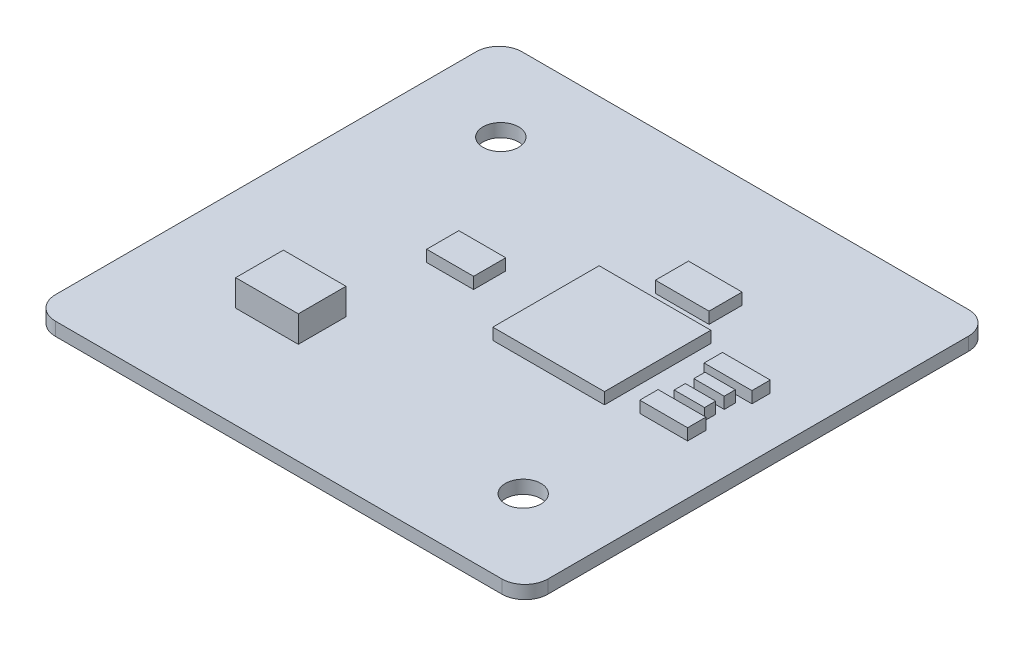
SolidWorks part; units mm, degrees
ref_plane "Front Plane" through (0, 0, 0) normal (0, 0, 1) x (1, 0, 0)
ref_plane "Top Plane" through (0, 0, 0) normal (0, 1, 0) x (1, 0, 0)
ref_plane "Right Plane" through (0, 0, 0) normal (1, 0, 0) x (0, 0, -1)
sketch "Sketch1" plane through (0, 0, 0) normal (0, 1, 0) x (1, 0, 0)
  line L1 (-19.425, 20.3) -> (19.425, 20.3)
  line L2 (-21.425, 18.3) -> (-21.425, -18.3)
  line L3 (-19.425, -20.3) -> (19.425, -20.3)
  line L4 (21.425, 18.3) -> (21.425, -18.3)
  line L5 (-21.425, 20.3) -> (21.425, -20.3) construction
  line L6 (-21.425, -20.3) -> (21.425, 20.3) construction
  arc A0 (19.425, -20.3) -> (21.425, -18.3) centre (19.425, -18.3) ccw
  arc A1 (19.425, 20.3) -> (21.425, 18.3) centre (19.425, 18.3) cw
  arc A2 (-21.425, -18.3) -> (-19.425, -20.3) centre (-19.425, -18.3) ccw
  arc A3 (-19.425, 20.3) -> (-21.425, 18.3) centre (-19.425, 18.3) ccw
  point P0 (0, 0)
  dimension "D3" = 2
  dimension "D1" = 42.85
  dimension "D2" = 40.6
extrude "Boss-Extrude1" add sketch "Sketch1" along normal blind 1.15
sketch "Sketch2" plane through (0, 1.15, 0) normal (0, 1, 0) x (1, 0, 0)
  line L0 (-21.425, 18.3) -> (-21.425, -18.3) construction
  line L1 (19.425, 20.3) -> (-19.425, 20.3) construction
  line L2 (0, 0) -> (18.8786, 20.3) construction
  line L3 (-21.425, 0) -> (21.425, 0) construction
  line L4 (21.425, -18.3) -> (21.425, 18.3) construction
  line L5 (0, 20.3) -> (0, -20.3) construction
  line L6 (-19.425, -20.3) -> (19.425, -20.3) construction
  line L7 (-13.925, 12.95) -> (0, 0) construction
  circle A0 centre (-13.925, 12.95) radius 1.55
  circle A1 centre (13.925, -12.95) radius 1.55
  dimension "D1" = 3.1
  dimension "D2" = 7.5
  dimension "D3" = 7.35
extrude "Cut-Extrude1" cut sketch "Sketch2" against normal up to next
sketch "Sketch3" plane through (0, 1.15, 0) normal (0, 1, 0) x (1, 0, 0)
  line L0 (-21.425, 18.3) -> (-21.425, -18.3) construction
  line L1 (-12.565, -7.33) -> (-7.115, -7.33)
  line L2 (-12.565, -7.33) -> (-12.565, -11.48)
  line L3 (-12.565, -11.48) -> (-7.115, -11.48)
  line L4 (-7.115, -7.33) -> (-7.115, -11.48)
  line L5 (-19.425, -20.3) -> (19.425, -20.3) construction
  dimension "D1" = 5.45
  dimension "D2" = 4.15
  dimension "D3" = 8.86
  dimension "D4" = 8.82
extrude "Boss-Extrude2" add sketch "Sketch3" along normal blind 2.3
sketch "Sketch4" plane through (0, 1.15, 0) normal (0, 1, 0) x (1, 0, 0)
  line L1 (1.0496, -2.7212) -> (10.7683, -2.7212)
  line L2 (1.0496, -2.7212) -> (1.0496, 6.5309)
  line L3 (1.0496, 6.5309) -> (10.7683, 6.5309)
  line L4 (10.7683, -2.7212) -> (10.7683, 6.5309)
  line L5 (4.5872, 10.7683) -> (9.2522, 10.7683)
  line L6 (4.5872, 10.7683) -> (4.5872, 7.8916)
  line L7 (4.5872, 7.8916) -> (9.2522, 7.8916)
  line L8 (9.2522, 10.7683) -> (9.2522, 7.8916)
  line L9 (-7.6972, 3.0711) -> (-3.6153, 3.0711)
  line L10 (-7.6972, 3.0711) -> (-7.6972, 0.2721)
  line L11 (-7.6972, 0.2721) -> (-3.6153, 0.2721)
  line L12 (-3.6153, 3.0711) -> (-3.6153, 0.2721)
  line L13 (12.9453, 5.3647) -> (17.1048, 5.3647)
  line L14 (12.9453, 5.3647) -> (12.9453, 3.7708)
  line L15 (12.9453, 3.7708) -> (17.1048, 3.7708)
  line L16 (17.1048, 5.3647) -> (17.1048, 3.7708)
  line L17 (13.6782, 3.1155) -> (16.3217, 3.1155)
  line L18 (13.6782, 3.1155) -> (13.6782, 2.1437)
  line L19 (13.6782, 2.1437) -> (16.3217, 2.1437)
  line L20 (16.3217, 3.1155) -> (16.3217, 2.1437)
  line L21 (13.6782, 1.405) -> (16.3217, 1.405)
  line L22 (13.6782, 1.405) -> (13.6782, 0.4332)
  line L23 (13.6782, 0.4332) -> (16.3217, 0.4332)
  line L24 (16.3217, 1.405) -> (16.3217, 0.4332)
  line L25 (12.9453, -0.2332) -> (17.1048, -0.2332)
  line L26 (12.9453, -0.2332) -> (12.9453, -1.8271)
  line L27 (12.9453, -1.8271) -> (17.1048, -1.8271)
  line L28 (17.1048, -0.2332) -> (17.1048, -1.8271)
extrude "Boss-Extrude3" add sketch "Sketch4" along normal blind 1
